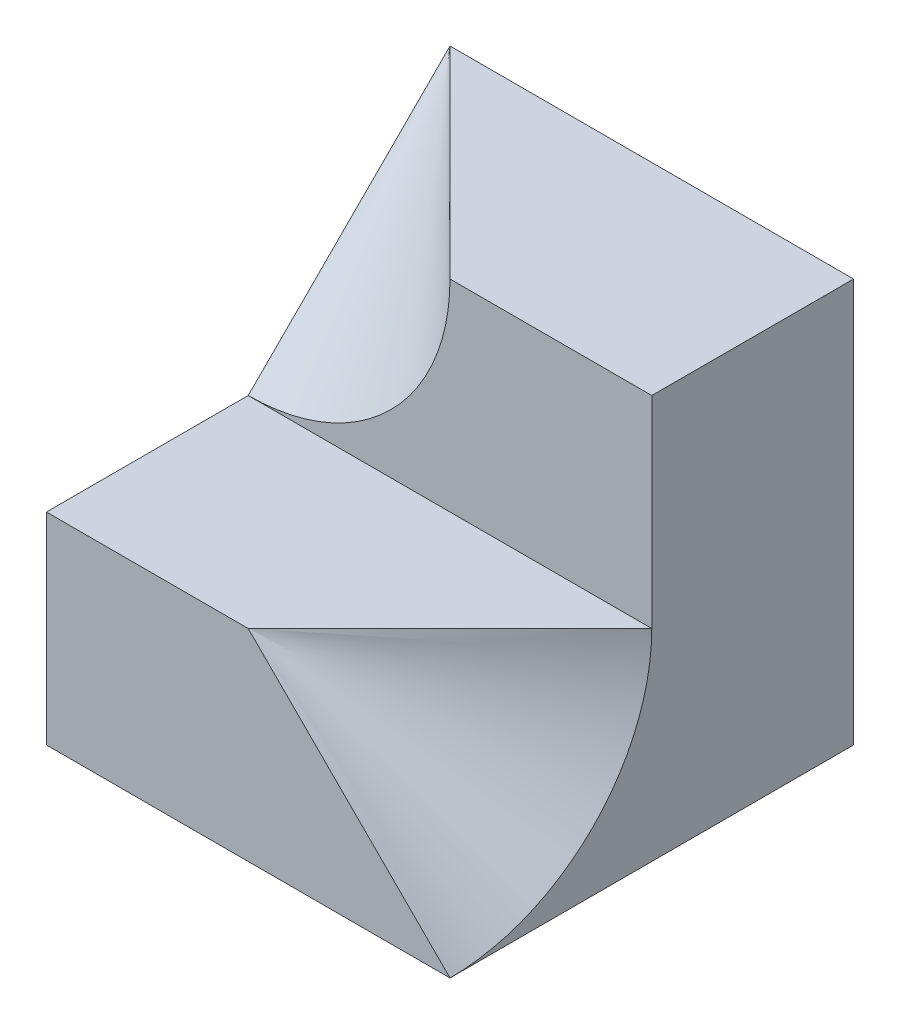
SolidWorks part; units mm, degrees
ref_plane "Front" through (0, 0, 0) normal (0, 0, 1) x (1, 0, 0)
ref_plane "Top" through (0, 0, 0) normal (0, 1, 0) x (1, 0, 0)
ref_plane "Right" through (0, 0, 0) normal (1, 0, 0) x (0, 0, -1)
sketch "Sketch1" plane through (0, 0, 0) normal (0, 1, 0) x (1, 0, 0)
  line L1 (0, 0) -> (4, 0)
  line L2 (0, 0) -> (0, 4)
  line L3 (0, 4) -> (4, 4)
  line L4 (4, 0) -> (4, 4)
  dimension "D1" = 4
  dimension "D2" = 4
extrude "Boss-Extrude1" add sketch "Sketch1" along normal blind 4
sketch "Sketch2" plane through (0, 0, 0) normal (-1, 0, 0) x (0, 0, 1)
  line L0 (-4, 4) -> (0, 4) construction
  line L1 (-2, 4) -> (0, 4)
  line L2 (-2, 4) -> (-2, 2)
  line L3 (-2, 2) -> (0, 2)
  line L4 (0, 4) -> (0, 2)
  line L5 (0, 4) -> (0, 0) construction
extrude "Cut-Extrude1" cut sketch "Sketch2" against normal blind 4
sketch "Sketch3" plane through (0, 0, 0) normal (-1, 0, 0) x (0, 0, 1)
  line L0 (-2, 2) -> (-4, 4)
  line L1 (-4, 4) -> (-2, 4)
  line L2 (-2, 4) -> (-2, 2)
revolve "Cut-Revolve1" cut sketch "Sketch3" angle 360 about L1
sketch "Sketch4" plane through (0, 0, 0) normal (0, 0, 1) x (1, 0, 0)
  line L0 (2, 2) -> (4, 0)
  line L1 (4, 2) -> (0, 2) construction
  line L2 (4, 0) -> (4, 2)
  line L3 (4, 2) -> (4, 0) construction
  line L4 (4, 2) -> (2, 2)
revolve "Cut-Revolve2" cut sketch "Sketch4" angle 360 about L4
